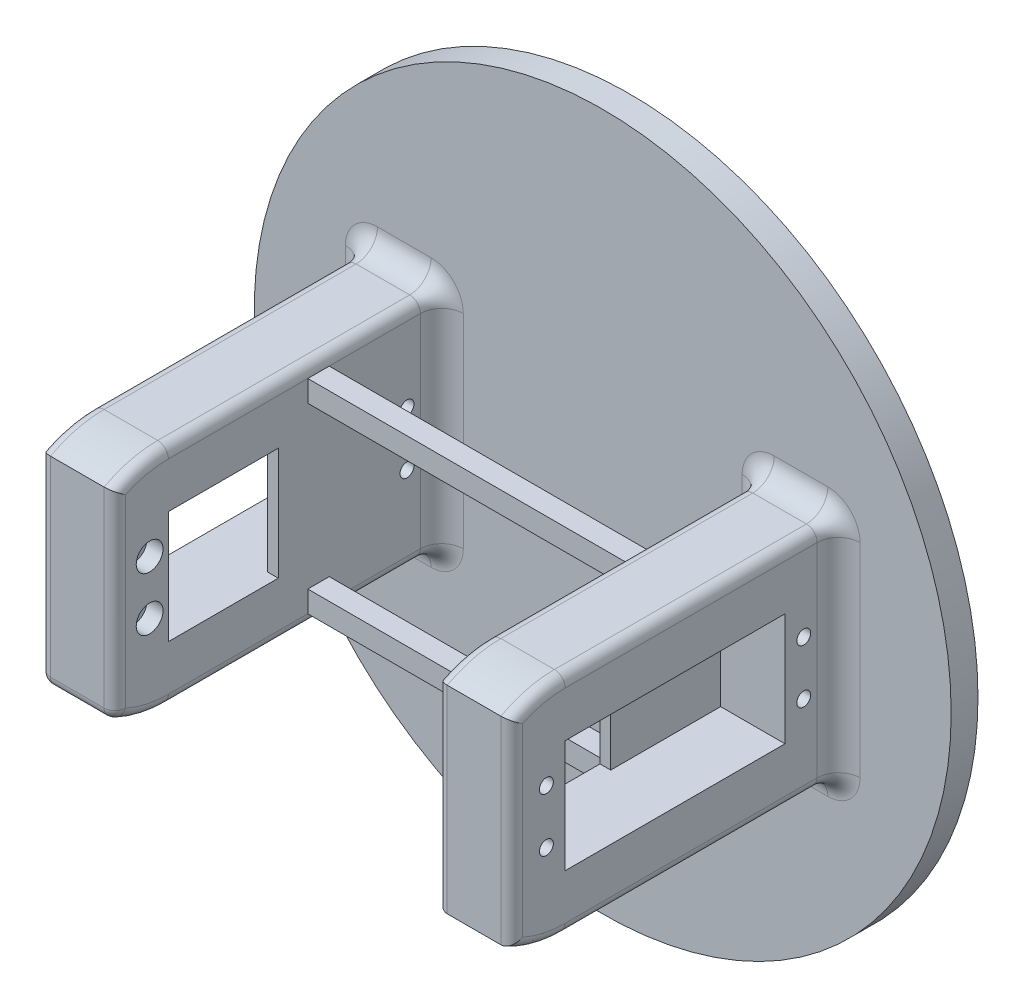
SolidWorks part; units mm, degrees
ref_plane "Front Plane" through (0, 0, 0) normal (0, 0, 1) x (1, 0, 0)
ref_plane "Top Plane" through (0, 0, 0) normal (0, 1, 0) x (1, 0, 0)
ref_plane "Right Plane" through (0, 0, 0) normal (1, 0, 0) x (0, 0, -1)
sketch "Sketch1" plane through (0, 0, 0) normal (0, 0, 1) x (1, 0, 0)
  circle A0 centre (0, 0) radius 65
  dimension "D1" = 130
extrude "Boss-Extrude1" add sketch "Sketch1" along normal blind 5
sketch "Sketch2" plane through (0, 0, 5) normal (0, 0, 1) x (1, 0, 0)
  line L0 (0, 88.8868) -> (0, -71.0654) construction
  line L1 (-44, 35) -> (-30, 35)
  line L2 (-44, 35) -> (-44, -35)
  line L3 (-44, -35) -> (-30, -35)
  line L4 (-30, 35) -> (-30, -35)
  line L5 (44, -35) -> (30, -35)
  line L6 (30, 35) -> (30, -35)
  line L7 (44, 35) -> (30, 35)
  line L8 (44, 35) -> (44, -35)
  dimension "D1" = 30
  dimension "D2" = 14
  dimension "D3" = 35
  dimension "D4" = 70
extrude "Boss-Extrude2" add sketch "Sketch2" along normal blind 70
sketch "Sketch4" plane through (-44, 0, 0) normal (-1, 0, 0) x (0, 0, 1)
  line L0 (5, 35) -> (5, -35) construction
  line L1 (15, -10.5) -> (56, -10.5)
  line L2 (15, -10.5) -> (15, 10.5)
  line L3 (15, 10.5) -> (56, 10.5)
  line L4 (56, -10.5) -> (56, 10.5)
  line L5 (15, -10.5) -> (56, 10.5) construction
  line L6 (15, 10.5) -> (56, -10.5) construction
  point P0 (35.5, 0)
  dimension "D1" = 10
  dimension "D2" = 41
  dimension "D3" = 21
extrude "Cut-Extrude1" cut sketch "Sketch4" against normal blind 12
sketch "Sketch5" plane through (-44, 0, 0) normal (-1, 0, 0) x (0, 0, 1)
  line L0 (5, 35) -> (5, -35) construction
  line L1 (5, 21) -> (56, 21)
  line L2 (5, 21) -> (5, -21)
  line L3 (5, -21) -> (56, -21)
  line L4 (56, 21) -> (56, -21)
  line L5 (56, -10.5) -> (56, 10.5) construction
  line L6 (75, 35) -> (5, 35) construction
  line L7 (75, -35) -> (5, -35) construction
  line L9 (66, 18.4662) -> (66, -18.4662)
  line L13 (5, 35) -> (5, -35)
  line L14 (5, -35) -> (75, -35)
  line L15 (75, -35) -> (75, 35)
  line L16 (75, 35) -> (5, 35)
  line L17 (5, 35) -> (5, -35)
  line L18 (5, -35) -> (75, -35)
  line L19 (75, -35) -> (75, 35)
  line L20 (75, 35) -> (5, 35)
  arc A0 (75, 8.9443) -> (75, -8.9443) centre (56, 0) ccw
  line M10 (5, 35) -> (5, -35)
  line M11 (5, -35) -> (75, -35)
  line M12 (75, -35) -> (75, 35)
  line M13 (75, 35) -> (5, 35)
  dimension "D1" = 14
  dimension "D2" = 14
  dimension "D4" = 10
  dimension "D3" = 0
extrude "Cut-Extrude2" cut sketch "Sketch5" against normal up to next (14 mm away) contours A0 L3 M10 M11 M12 | A0 L1 M12 M13 M10 | L9 A0 L19
fillet "Fillet1" radius 2 11 edges at (-30, 20.3567, 61.158) (-30, -20.3567, 61.158) (-44, -20.3567, 61.158) (-44, 21, 30.5) (-30, 0, 66) (-30, 21, 30.5) (-30, -21, 30.5) (-44, -21, 30.5) (-44, 20.3567, 61.158) (-37, -18.4662, 66) (-44, 0, 66)
fillet "Fillet2" radius 4 8 edges at (-43.4142, 20.4142, 5) (-37, 21, 5) (-30.5858, 20.4142, 5) (-30, 0, 5) (-30.5858, -20.4142, 5) (-37, -21, 5) (-43.4142, -20.4142, 5) (-44, 0, 5)
mirror "Mirror2" about plane through (0, 0, 0) normal (1, 0, 0) of "Cut-Extrude1"
mirror "Mirror3" about plane through (0, 0, 0) normal (1, 0, 0) of "Cut-Extrude2"
fillet "Fillet3" radius 2 10 edges at (30, 20.3567, 61.158) (30, -20.3567, 61.158) (44, 20.3567, 61.158) (44, -20.3567, 61.158) (30, 21, 30.5) (30, -21, 30.5) (30, 0, 66) (44, 21, 30.5) (44, 0, 66) (44, -21, 30.5)
fillet "Fillet4" radius 4 8 edges at (43.4142, -20.4142, 5) (37, -21, 5) (30.5858, -20.4142, 5) (30, 0, 5) (30.5858, 20.4142, 5) (37, 21, 5) (43.4142, 20.4142, 5) (44, 0, 5)
sketch "Sketch7" plane through (-44, 0, 0) normal (-1, 0, 0) x (0, 0, 1)
  line L0 (71.8559, 0) -> (-5.9033, 0) construction
  line L1 (56, -10.5) -> (56, 10.5) construction
  line L2 (35.5, 19) -> (35.5, -19) construction
  line L3 (56, 19) -> (9, 19) construction
  line L4 (9, -19) -> (56, -19) construction
  line L5 (15, 10.5) -> (15, -10.5) construction
  circle A0 centre (59.5, 5) radius 1.3
  circle A1 centre (59.5, -5) radius 1.3
  circle A2 centre (11.5, -5) radius 1.3
  circle A3 centre (11.5, 5) radius 1.3
  dimension "D1" = 2.6
  dimension "D2" = 3.5
  dimension "D3" = 5
extrude "Cut-Extrude3" cut sketch "Sketch7" against normal up to next (14 mm away)
mirror "Mirror6" about plane through (0, 0, 0) normal (1, 0, 0) of "Cut-Extrude3"
sketch "Sketch8" plane through (-32, 0, 0) normal (-1, 0, 0) x (0, 0, 1)
  line L0 (15, -10.5) -> (56, -10.5) construction
  line L1 (56, 10.5) -> (35.5, 10.5)
  line L2 (56, 10.5) -> (56, -10.5)
  line L3 (56, -10.5) -> (35.5, -10.5)
  line L4 (35.5, 10.5) -> (35.5, -10.5)
extrude "Cut-Extrude4" cut sketch "Sketch8" against normal up to next (2 mm away)
mirror "Mirror7" about plane through (0, 0, 0) normal (1, 0, 0) of "Cut-Extrude4"
ref_plane "Plane1" through (0, 0, 30) normal (0, 0, 1) x (1, 0, 0)
sketch "Sketch9" plane through (0, 0, 30) normal (0, 0, 1) x (1, 0, 0)
  line L0 (30, 19) -> (30, -19) construction
  line L1 (-30, -19) -> (30, -19)
  line L2 (-30, -19) -> (-30, -15)
  line L3 (-30, -15) -> (30, -15)
  line L4 (30, -19) -> (30, -15)
  dimension "D1" = 4
extrude "Boss-Extrude3" add sketch "Sketch9" against normal blind 4
mirror "Mirror8" about plane through (0, 0, 0) normal (0, 1, 0) of "Boss-Extrude3"
sketch "Sketch10" plane through (-30, 0, 0) normal (1, 0, 0) x (0, 0, -1)
  circle A0 centre (-59.5, -5) radius 1.3 construction
  circle A1 centre (-59.5, 5) radius 1.3 construction
  circle A2 centre (-59.5, -5) radius 1.3
  circle A3 centre (-59.5, 5) radius 1.3
  circle A4 centre (-59.5, 5) radius 2.5
  circle A5 centre (-59.5, -5) radius 2.5
  dimension "D1" = 5
  dimension "D2" = 5
extrude "Cut-Extrude5" cut sketch "Sketch10" against normal blind 3
mirror "Mirror9" about plane through (0, 0, 0) normal (1, 0, 0) of "Cut-Extrude5"
